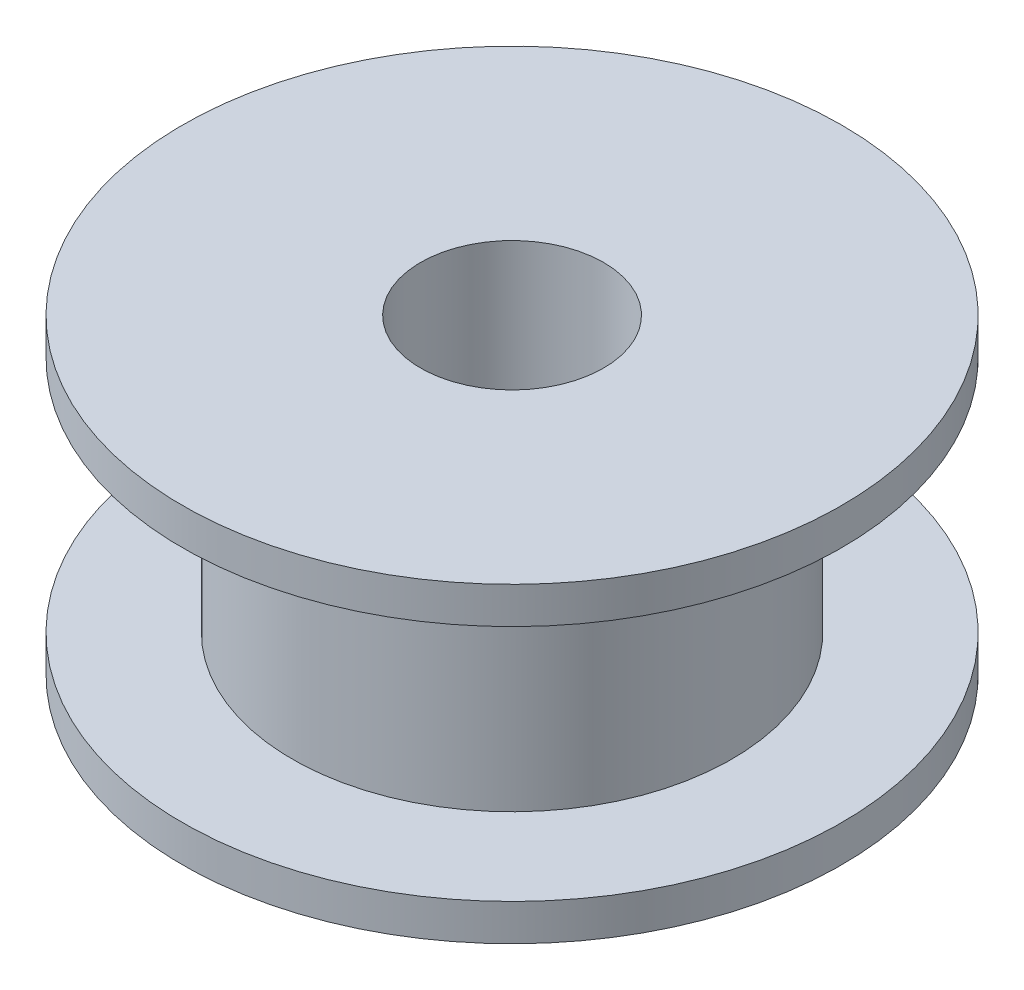
SolidWorks part; units mm, degrees
ref_plane "Plan de face" through (0, 0, 0) normal (0, 0, 1) x (1, 0, 0)
ref_plane "Plan de dessus" through (0, 0, 0) normal (0, 1, 0) x (1, 0, 0)
ref_plane "Plan de droite" through (0, 0, 0) normal (1, 0, 0) x (0, 0, -1)
sketch "Esquisse1" plane through (0, 0, 0) normal (0, 0, 1) x (1, 0, 0)
  line L0 (-6, 7.5) -> (-6, 1)
  line L1 (-2.5, 0) -> (-6, 0)
  line L2 (-2.5, 0) -> (-2.5, 8.5)
  line L3 (-2.5, 8.5) -> (-6, 8.5)
  line L4 (-6, 0) -> (-6, 8.5) construction
  line L5 (-6, 8.5) -> (-9, 8.5)
  line L6 (-6, 8.5) -> (-6, 7.5) construction
  line L7 (-6, 7.5) -> (-9, 7.5)
  line L8 (-9, 8.5) -> (-9, 7.5)
  line L9 (-6, 0) -> (-9, 0)
  line L10 (-6, 0) -> (-6, 1) construction
  line L11 (-6, 1) -> (-9, 1)
  line L12 (-9, 0) -> (-9, 1)
  line L13 (0, 0) -> (0, 8.5) construction
  dimension "D1" = 2.5
  dimension "D2" = 6
  dimension "D3" = 9
  dimension "D4" = 8.5
  dimension "D5" = 6.5
revolve "Révolution1" add sketch "Esquisse1" angle 360 about L13
